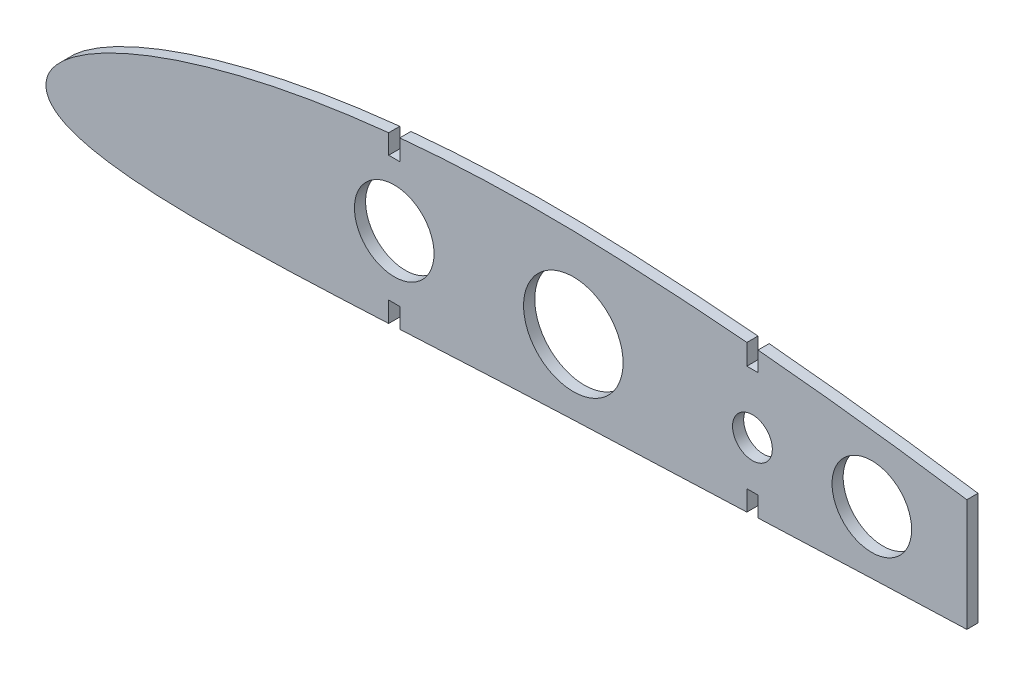
SolidWorks part; units mm, degrees
material "Сосна обыкновенная"
ref_plane "Front Plane" through (0, 0, 0) normal (0, 0, 1) x (1, 0, 0)
ref_plane "Top Plane" through (0, 0, 0) normal (0, 1, 0) x (1, 0, 0)
ref_plane "Right Plane" through (0, 0, 0) normal (1, 0, 0) x (0, 0, -1)
curve "Кривая1"
  spline degree 3 poles (0.0672, 0.87, 0) (0.0318, 0.5229, 0) (-0.0389, -0.1715, 0) (0.1092, -1.2382, 0) (0.4896, -2.2944, 0) (1.1401, -3.3111, 0) (2.0489, -4.255, 0) (3.2074, -5.1254, 0) (4.6283, -5.9301, 0) (6.3494, -6.6831, 0) (8.4416, -7.3951, 0) (11.0166, -8.0714, 0) (14.2364, -8.7104, 0) (18.3056, -9.2955, 0) (23.4194, -9.7901, 0) (29.6659, -10.1463, 0) (36.96, -10.3273, 0) (45.0764, -10.3268, 0) (53.7569, -10.166, 0) (62.8007, -9.8793, 0) (72.0812, -9.501, 0) (81.5234, -9.0613, 0) (91.0729, -8.586, 0) (100.6751, -8.0976, 0) (110.2799, -7.6156, 0) (119.8547, -7.1553, 0) (129.405, -6.7269, 0) (138.957, -6.3448, 0) (148.5363, -5.9896, 0) (158.1569, -5.6043, 0) (167.8102, -5.2124, 0) (177.4834, -4.8161, 0) (187.1542, -4.4222, 0) (196.8146, -4.0353, 0) (206.4608, -3.6595, 0) (216.0936, -3.2979, 0) (225.7151, -2.9531, 0) (235.3272, -2.6273, 0) (244.9322, -2.3221, 0) (254.532, -2.0389, 0) (264.1285, -1.7785, 0) (273.7233, -1.5416, 0) (283.3173, -1.3281, 0) (292.9097, -1.138, 0) (302.4935, -0.971, 0) (312.041, -0.8264, 0) (321.4647, -0.7041, 0) (330.5223, -0.6041, 0) (338.7731, -0.5271, 0) (345.1826, -0.4754, 0) (348.7687, -0.4498, 0) (350, -0.441, 0) knots 0 0 0 0 0.002941 0.005884 0.009016 0.012365 0.016008 0.020037 0.024574 0.029784 0.035897 0.04324 0.052276 0.063635 0.077983 0.095698 0.11652 0.139661 0.164312 0.189919 0.216157 0.242838 0.269834 0.296993 0.324123 0.351139 0.378036 0.404946 0.431961 0.459078 0.486347 0.513641 0.540929 0.568176 0.59538 0.622543 0.649673 0.676775 0.703855 0.730919 0.757971 0.785018 0.812062 0.839103 0.866132 0.893099 0.919831 0.94581 0.969681 0.98959 1 1 1 1
curve "Кривая2"
  spline degree 3 poles (350, 0.441, 0) (348.8179, 0.763, 0) (345.4082, 1.6919, 0) (339.3479, 3.3017, 0) (331.5897, 5.3027, 0) (323.0919, 7.4172, 0) (314.2383, 9.538, 0) (305.2428, 11.6083, 0) (296.1874, 13.6076, 0) (287.1014, 15.5293, 0) (277.9952, 17.371, 0) (268.8733, 19.1314, 0) (259.7387, 20.8097, 0) (250.5935, 22.4048, 0) (241.4399, 23.9153, 0) (232.28, 25.3398, 0) (223.1162, 26.6763, 0) (213.9505, 27.9228, 0) (204.7856, 29.077, 0) (195.6239, 30.1359, 0) (186.4686, 31.0968, 0) (177.3222, 31.956, 0) (168.1915, 32.7096, 0) (159.08, 33.3545, 0) (150.0138, 33.8803, 0) (141.0375, 34.2978, 0) (132.1765, 34.5613, 0) (123.4183, 34.6361, 0) (114.7287, 34.5224, 0) (106.0927, 34.2174, 0) (97.5152, 33.7146, 0) (89.0056, 33.0092, 0) (80.5773, 32.0949, 0) (72.2481, 30.9667, 0) (64.0422, 29.6192, 0) (55.9942, 28.0495, 0) (48.1571, 26.2588, 0) (40.6145, 24.2587, 0) (33.4961, 22.0806, 0) (26.979, 19.788, 0) (21.2507, 17.4767, 0) (16.4367, 15.2539, 0) (12.5431, 13.2014, 0) (9.4652, 11.352, 0) (7.0472, 9.6945, 0) (5.1404, 8.1959, 0) (3.6289, 6.8198, 0) (2.4334, 5.5336, 0) (1.4978, 4.3133, 0) (0.8003, 3.1383, 0) (0.3021, 2.0031, 0) (0.1432, 1.2365, 0) (0.0672, 0.87, 0) knots 0 0 0 0 0.010162 0.029313 0.052012 0.076619 0.101948 0.127526 0.153184 0.178868 0.204558 0.230246 0.255926 0.281594 0.307246 0.332878 0.358485 0.384061 0.409603 0.435104 0.460559 0.485959 0.511303 0.536552 0.561723 0.586629 0.611085 0.635251 0.659272 0.683164 0.706922 0.730536 0.753983 0.777235 0.800246 0.822951 0.845237 0.866916 0.887662 0.906968 0.924203 0.938879 0.950932 0.960693 0.968647 0.975233 0.980795 0.985584 0.989782 0.993521 0.996902 1 1 1 1
sketch "Эскиз2" plane through (0, 0, 0) normal (0, 0, 1) x (1, 0, 0)
  line L1 (0, 0) -> (0, 59.698) construction
  line L2 (0, 0) -> (231.3768, 0) construction
  line L3 (87.5, 77.9689) -> (87.5, 51.797) construction
  line L5 (48.6093, 12.0313) -> (232.4701, 12.0313) construction
  line L10 (87.5, 32.8256) -> (87.5, -53.7006) construction
  line L12 (86.1, 32.6823) -> (86.1, 27.7856)
  line L13 (86.1, 27.7856) -> (88.9, 27.7856)
  line L14 (88.9, 32.963) -> (88.9, 27.7856)
  line L15 (87.5, 32.8256) -> (88.9, 27.7856) construction
  line L16 (86.1, 27.7856) -> (87.5, 32.8256) construction
  line L17 (177.5, 12.0313) -> (177.5, 39.9872) construction
  line L18 (177.5, 12.0313) -> (177.5, -23.4861) construction
  line L19 (176.1, 26.8829) -> (178.9, 26.8829)
  line L20 (176.1, 26.8829) -> (176.1, 32.0455)
  line L22 (178.9, 26.8829) -> (178.9, 31.7979)
  line L23 (176.1, 26.8829) -> (177.5, 31.9229) construction
  line L24 (177.5, 31.9229) -> (178.9, 26.8829) construction
  line L26 (86.1, -8.8326) -> (86.1, -3.7231)
  line L27 (86.1, -3.7231) -> (88.9, -3.7231)
  line L28 (88.9, -8.6933) -> (88.9, -3.7231)
  line L29 (87.5, -8.7631) -> (88.9, -3.7231) construction
  line L30 (86.1, -3.7231) -> (87.5, -8.7631) construction
  line L31 (231.3768, 25.4607) -> (231.3768, -2.7621)
  line L33 (176.1, -4.873) -> (176.1, 0.2242)
  line L34 (176.1, 0.2242) -> (178.9, 0.2242)
  line L35 (178.9, -4.7586) -> (178.9, 0.2242)
  line L36 (177.5, -4.8158) -> (178.9, 0.2242) construction
  line L37 (176.1, 0.2242) -> (177.5, -4.8158) construction
  circle A5 centre (87.5, 12.0313) radius 10
  circle A6 centre (177.5, 12.0313) radius 5
  circle A7 centre (132.5, 12.0313) radius 12.5
  circle A8 centre (207.5, 12.0313) radius 10
  spline S1 degree 3 poles (231.3768, 25.4607) (228.6231, 25.873) (222.8162, 26.7171) (213.9505, 27.9228) (204.7856, 29.077) (195.6239, 30.1359) (186.9965, 31.0414) (181.4212, 31.5705) (178.9, 31.7979) knots 0.335389 0.335389 0.335389 0.335389 0.358485 0.384061 0.409603 0.435104 0.460559 0.481556 0.481556 0.481556 0.481556
  spline S2 degree 3 poles (0.0672, 0.87) (0.0318, 0.5229) (-0.0389, -0.1715) (0.1092, -1.2382) (0.4896, -2.2944) (1.1401, -3.3111) (2.0489, -4.255) (3.2074, -5.1254) (4.6283, -5.9301) (6.3494, -6.6831) (8.4416, -7.3951) (11.0166, -8.0714) (14.2364, -8.7104) (18.3056, -9.2955) (23.4194, -9.7901) (29.6659, -10.1463) (36.96, -10.3273) (45.0764, -10.3268) (53.7569, -10.166) (62.8007, -9.8793) (72.0812, -9.501) (79.8719, -9.1382) (84.562, -8.9087) (86.1, -8.8326) knots 0 0 0 0 0.002941 0.005884 0.009016 0.012365 0.016008 0.020037 0.024574 0.029784 0.035897 0.04324 0.052276 0.063635 0.077983 0.095698 0.11652 0.139661 0.164312 0.189919 0.216157 0.242838 0.255856 0.255856 0.255856 0.255856
  spline S4 degree 3 poles (88.9, -8.6933) (89.6178, -8.6574) (93.5441, -8.4603) (100.6751, -8.0976) (110.2799, -7.6156) (119.8547, -7.1553) (129.405, -6.7269) (138.957, -6.3448) (148.5363, -5.9896) (158.1569, -5.6043) (167.3488, -5.2312) (173.3358, -4.986) (176.1, -4.873) knots 0.263757 0.263757 0.263757 0.263757 0.269834 0.296993 0.324123 0.351139 0.378036 0.404946 0.431961 0.459078 0.486347 0.509737 0.509737 0.509737 0.509737
  spline S5 degree 3 poles (86.1, 32.6823) (84.251, 32.489) (79.6181, 31.965) (72.2481, 30.9667) (64.0422, 29.6192) (55.9942, 28.0495) (48.1571, 26.2588) (40.6145, 24.2587) (33.4961, 22.0806) (26.979, 19.788) (21.2507, 17.4767) (16.4367, 15.2539) (12.5431, 13.2014) (9.4652, 11.352) (7.0472, 9.6945) (5.1404, 8.1959) (3.6289, 6.8198) (2.4334, 5.5336) (1.4978, 4.3133) (0.8003, 3.1383) (0.3021, 2.0031) (0.1432, 1.2365) (0.0672, 0.87) knots 0.738563 0.738563 0.738563 0.738563 0.753983 0.777235 0.800246 0.822951 0.845237 0.866916 0.887662 0.906968 0.924203 0.938879 0.950932 0.960693 0.968647 0.975233 0.980795 0.985584 0.989782 0.993521 0.996902 1 1 1 1
  spline S6 degree 3 poles (178.9, -4.7586) (181.653, -4.6463) (187.6262, -4.4033) (196.8146, -4.0353) (206.4608, -3.6595) (216.0936, -3.2979) (224.3975, -3.0003) (229.4906, -2.8257) (231.3768, -2.7621) knots 0.517634 0.517634 0.517634 0.517634 0.540929 0.568176 0.59538 0.622543 0.649673 0.665629 0.665629 0.665629 0.665629
  spline S7 degree 3 poles (176.1, 32.0455) (173.4606, 32.2744) (167.7863, 32.7382) (159.08, 33.3545) (150.0138, 33.8803) (141.0375, 34.2978) (132.1765, 34.5613) (123.4183, 34.6361) (114.7287, 34.5224) (106.0927, 34.2174) (97.4854, 33.7129) (91.7636, 33.2378) (88.9, 32.963) knots 0.489328 0.489328 0.489328 0.489328 0.511303 0.536552 0.561723 0.586629 0.611085 0.635251 0.659272 0.683164 0.706922 0.730783 0.730783 0.730783 0.730783
  point P14 (87.5, 32.8256)
  point P17 (87.5, -8.7631)
  point P26 (87.5, 32.8256)
  point P28 (177.5, 31.9229)
  point P35 (177.5, 31.9229)
  point P36 (87.5, -8.7631)
  point P42 (87.5, -8.7631)
  point P46 (177.5, -4.8158)
  point P49 (177.5, -4.8158)
  point P63 (231.3768, 25.4607)
  point P64 (231.3768, -2.7621)
  dimension "D5" = 20
  dimension "D8" = 10
  dimension "D10" = 25
  dimension "D12" = 20
  dimension "D3" = 87.5
  dimension "D6" = 41.5887
  dimension "D7" = 20.7944
  dimension "D9" = 90
  dimension "D11" = 45
  dimension "D13" = 30
  dimension "D14" = 2.8
  dimension "D15" = 1.4
  dimension "D16" = 5.04
  dimension "D17" = 2.8
  dimension "D18" = 1.4
  dimension "D19" = 5.04
  dimension "D20" = 2.8
  dimension "D21" = 5.04
  dimension "D22" = 1.4
  dimension "D23" = 2.8
  dimension "D24" = 5.04
  dimension "D25" = 1.4
extrude "Бобышка-Вытянуть1" add sketch "Эскиз2" along normal mid plane 2.8
equation "\"Thickness\"= 2.8"
equation "\"chord\"= 350"
equation "\"D3@Эскиз2\"=\"chord\"/4"
equation "\"D7@Эскиз2\"=\"D6@Эскиз2\"/2"
equation "\"D11@Эскиз2\"=\"D9@Эскиз2\"/2"
equation "\"D14@Эскиз2\"=\"Thickness\""
equation "\"D15@Эскиз2\"=\"D14@Эскиз2\"/2"
equation "\"D16@Эскиз2\"=\"Thickness\"*1.8"
equation "\"D17@Эскиз2\"=\"Thickness\""
equation "\"D18@Эскиз2\"=\"Thickness\"/2"
equation "\"D19@Эскиз2\"=\"Thickness\"*1.8"
equation "\"D20@Эскиз2\"=\"Thickness\""
equation "\"D21@Эскиз2\"=\"Thickness\"*1.8"
equation "\"D22@Эскиз2\"=\"Thickness\"/2"
equation "\"D23@Эскиз2\"=\"Thickness\""
equation "\"D24@Эскиз2\"=\"Thickness\"*1.8"
equation "\"D25@Эскиз2\"=\"Thickness\"/2"
